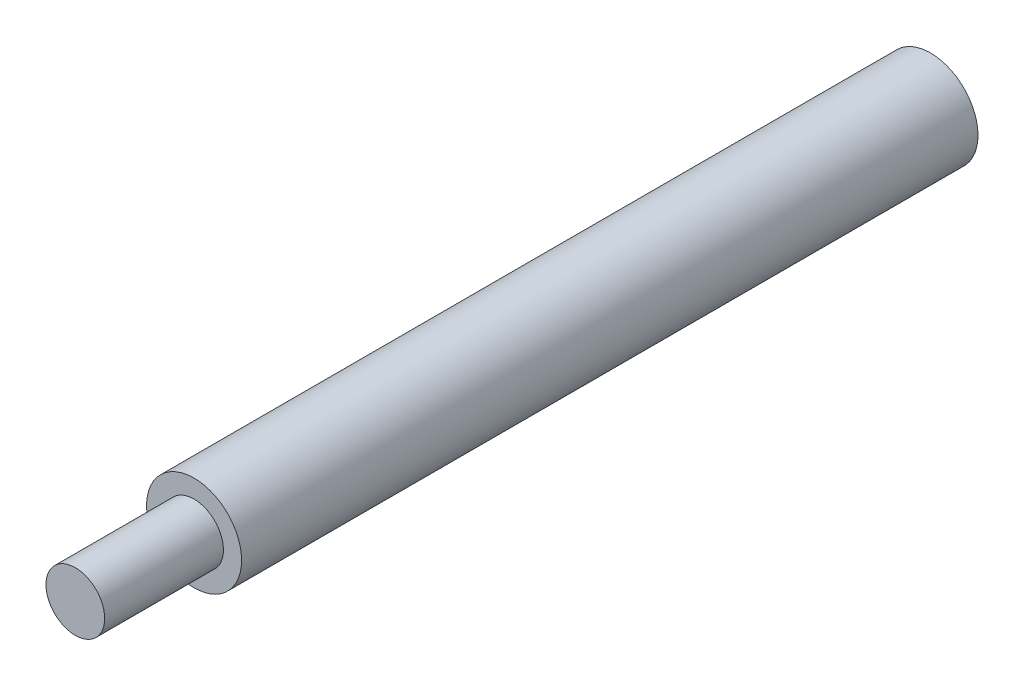
SolidWorks part; units mm, degrees
ref_plane "Front Plane" through (0, 0, 0) normal (0, 0, 1) x (1, 0, 0)
ref_plane "Top Plane" through (0, 0, 0) normal (0, 1, 0) x (1, 0, 0)
ref_plane "Right Plane" through (0, 0, 0) normal (1, 0, 0) x (0, 0, -1)
sketch "Sketch1" plane through (0, 0, 0) normal (0, 0, 1) x (1, 0, 0)
  circle A0 centre (0, 0) radius 4
  dimension "D1" = 8
extrude "Boss-Extrude1" add sketch "Sketch1" along normal blind 62
sketch "Sketch2" plane through (0, 0, 62) normal (0, 0, 1) x (1, 0, 0)
  circle A0 centre (0, 0) radius 2.4717
extrude "Boss-Extrude2" add sketch "Sketch2" along normal blind 10
